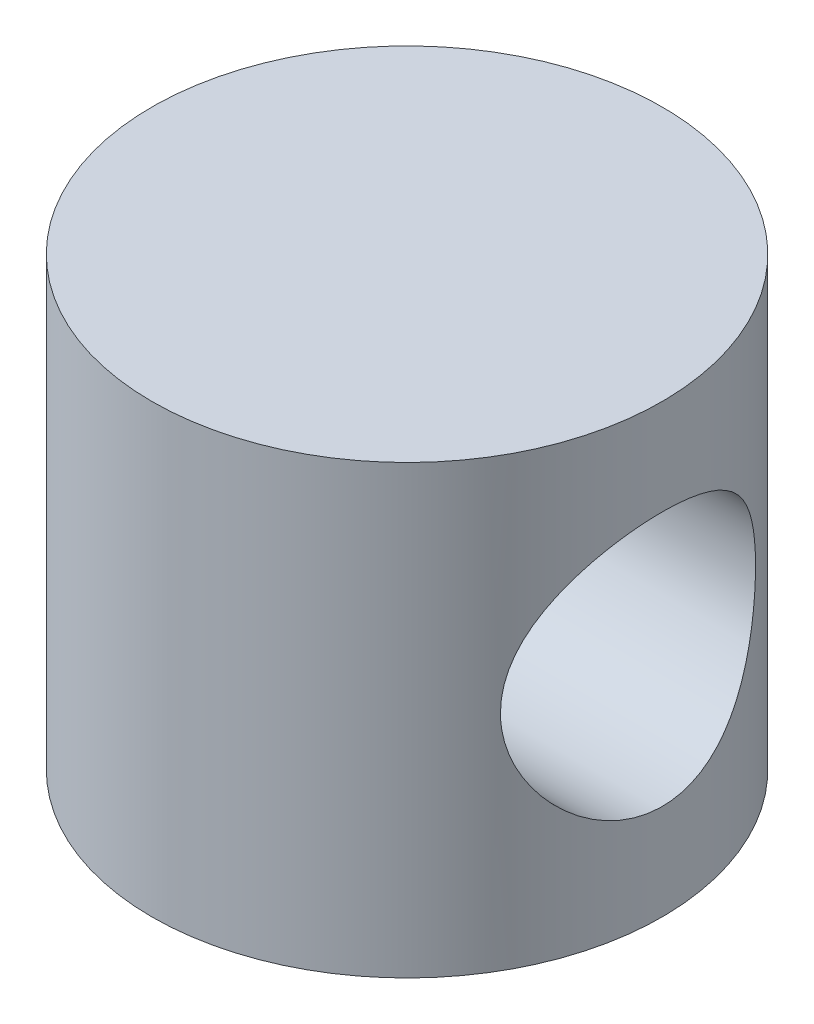
SolidWorks part; units mm, degrees
ref_plane "Front Plane" through (0, 0, 0) normal (0, 0, 1) x (1, 0, 0)
ref_plane "Top Plane" through (0, 0, 0) normal (0, 1, 0) x (1, 0, 0)
ref_plane "Right Plane" through (0, 0, 0) normal (1, 0, 0) x (0, 0, -1)
sketch "Sketch1" plane through (0, 0, 0) normal (0, 1, 0) x (1, 0, 0)
  circle A0 centre (0, 0) radius 8
extrude "Boss-Extrude1" add sketch "Sketch1" along normal blind 14
sketch "Sketch2" plane through (0, 14, 0) normal (0, 1, 0) x (1, 0, 0)
  line L2 (8, -8.5349) -> (-8, -8.5349)
  line L3 (8, -8.5349) -> (8, 8.5349)
  line L4 (8, 8.5349) -> (-8, 8.5349)
  line L5 (-8, -8.5349) -> (-8, 8.5349)
  line L6 (8, -8.5349) -> (-8, 8.5349) construction
  line L7 (8, 8.5349) -> (-8, -8.5349) construction
  point P0 (0, 0)
extrude "Boss-Extrude2" add sketch "Sketch2" along normal blind 7
sketch "Sketch3" plane through (-8, 0, 0) normal (-1, 0, 0) x (0, 0, 1)
  line L0 (-8, 0) -> (8, 0) construction
  circle A0 centre (0, 7) radius 4
  dimension "D1" = 7
extrude "Cut-Extrude1" cut sketch "Sketch3" against normal blind 29
sketch "Sketch4" plane through (-8, 0, 0) normal (-1, 0, 0) x (0, 0, 1)
  line L1 (8.5349, 21) -> (-8.5349, 21)
  line L2 (8.5349, 21) -> (8.5349, 14)
  line L3 (8.5349, 14) -> (-8.5349, 14)
  line L4 (-8.5349, 21) -> (-8.5349, 14)
extrude "Cut-Extrude2" cut sketch "Sketch4" against normal blind 29
